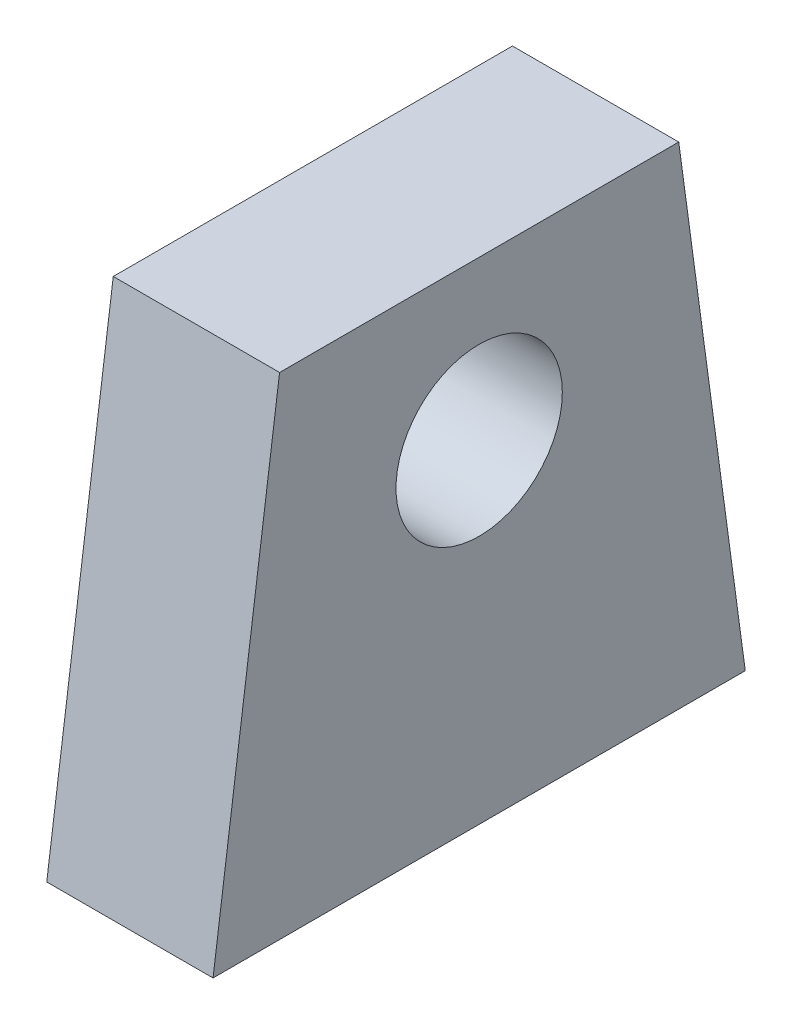
SolidWorks part; units mm, degrees
ref_plane "Front Plane" through (0, 0, 0) normal (0, 0, 1) x (1, 0, 0)
ref_plane "Top Plane" through (0, 0, 0) normal (0, 1, 0) x (1, 0, 0)
ref_plane "Right Plane" through (0, 0, 0) normal (1, 0, 0) x (0, 0, -1)
sketch "Sketch1" plane through (0, 0, 0) normal (1, 0, 0) x (0, 0, -1)
  line L0 (0, 2.5) -> (0, -10) construction
  line L1 (8, -10) -> (-8, -10)
  line L2 (-8, -10) -> (-6, 4.7653)
  line L3 (-6, 4.7653) -> (6, 4.7653)
  line L4 (8, -10) -> (6, 4.7653)
  line L5 (0, -2.5) -> (0, -10) construction
  circle A0 centre (0, 0) radius 2.5
  point P10 (0, 4.7653)
  dimension "D1" = 5
  dimension "D4" = 10
  dimension "D2" = 8
  dimension "D3" = 6
extrude "Boss-Extrude1" add sketch "Sketch1" along normal blind 5 contours L0 A0 | A0 L0 | L3 L4 L1 L2
